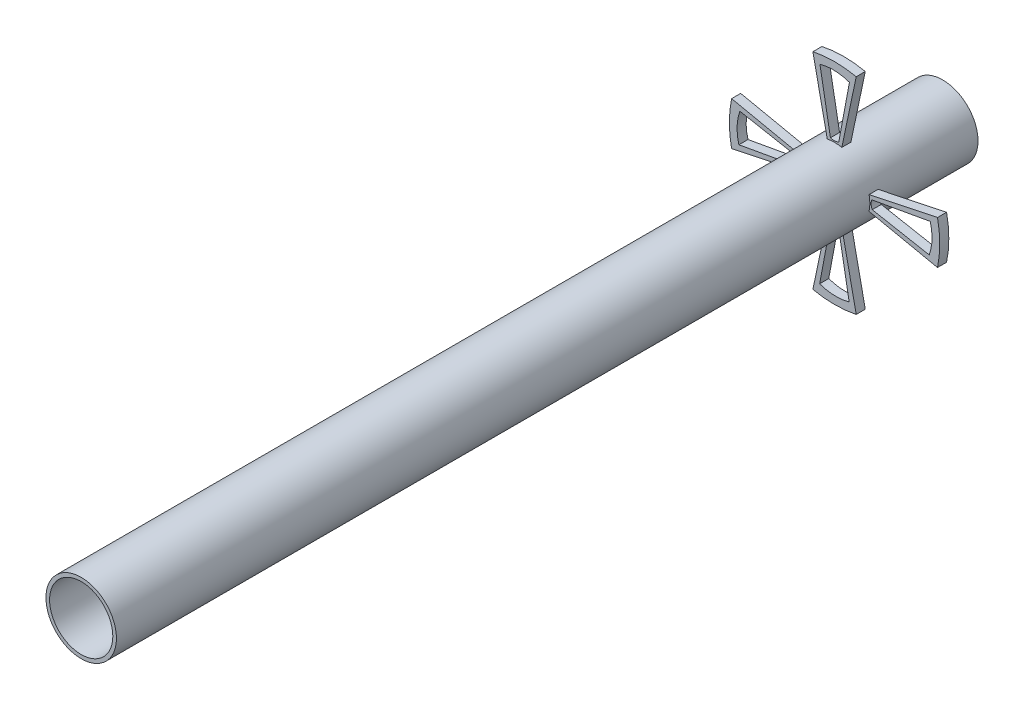
SolidWorks part; units mm, degrees
ref_plane "Front Plane" through (0, 0, 0) normal (0, 0, 1) x (1, 0, 0)
ref_plane "Top Plane" through (0, 0, 0) normal (0, 1, 0) x (1, 0, 0)
ref_plane "Right Plane" through (0, 0, 0) normal (1, 0, 0) x (0, 0, -1)
sketch "Sketch4" plane through (0, 0, 0) normal (0, 0, 1) x (1, 0, 0)
  line L0 (-95.0204, -20) -> (-283.5289, -59.6775)
  line L1 (-95.0204, 20) -> (-283.5289, 59.6775)
  line L2 (20, 95.0204) -> (59.6775, 283.5289)
  line L3 (-20, 95.0204) -> (-59.6775, 283.5289)
  line L4 (95.0204, -20) -> (283.5289, -59.6775)
  line L5 (95.0204, 20) -> (283.5289, 59.6775)
  line L6 (-20, -95.0204) -> (-59.6775, -283.5289)
  line L7 (20, -95.0204) -> (59.6775, -283.5289)
  line L8 (-102.4488, -11.3444) -> (-263.4403, -40.3434)
  line L9 (-103.7499, 11.6183) -> (-260.7282, 40.9886)
  line L10 (11.6183, 103.7499) -> (40.9886, 260.7282)
  line L11 (-11.3444, 102.4488) -> (-40.3434, 263.4403)
  line L12 (103.7499, -11.6183) -> (260.7282, -40.9886)
  line L13 (102.4488, 11.3444) -> (263.4403, 40.3434)
  line L14 (-11.6183, -103.7499) -> (-40.9886, -260.7282)
  line L15 (11.3444, -102.4488) -> (40.3434, -263.4403)
  arc A0 (-59.6775, -283.5289) -> (59.6775, -283.5289) centre (0, 0) ccw
  circle A1 centre (0, 0) radius 97.1024
  circle A2 centre (0, 0) radius 97.1024
  arc A3 (-59.6775, -283.5289) -> (59.6775, -283.5289) centre (0, 0) ccw
  circle A4 centre (0, 0) radius 97.1024
  arc A5 (-59.6775, -283.5289) -> (59.6775, -283.5289) centre (0, 0) ccw
  circle A6 centre (0, 0) radius 97.1024
  arc A7 (-59.6775, -283.5289) -> (59.6775, -283.5289) centre (0, 0) ccw
  arc A8 (-283.5289, 59.6775) -> (-283.5289, -59.6775) centre (0, 0) ccw
  arc A9 (-283.5289, 59.6775) -> (-283.5289, -59.6775) centre (0, 0) ccw
  arc A10 (-283.5289, 59.6775) -> (-283.5289, -59.6775) centre (0, 0) ccw
  arc A11 (-283.5289, 59.6775) -> (-283.5289, -59.6775) centre (0, 0) ccw
  arc A12 (59.6775, 283.5289) -> (-59.6775, 283.5289) centre (0, 0) ccw
  arc A13 (59.6775, 283.5289) -> (-59.6775, 283.5289) centre (0, 0) ccw
  arc A14 (59.6775, 283.5289) -> (-59.6775, 283.5289) centre (0, 0) ccw
  arc A15 (59.6775, 283.5289) -> (-59.6775, 283.5289) centre (0, 0) ccw
  arc A16 (283.5289, -59.6775) -> (283.5289, 59.6775) centre (0, 0) ccw
  arc A17 (283.5289, -59.6775) -> (283.5289, 59.6775) centre (0, 0) ccw
  arc A18 (283.5289, -59.6775) -> (283.5289, 59.6775) centre (0, 0) ccw
  arc A19 (283.5289, -59.6775) -> (283.5289, 59.6775) centre (0, 0) ccw
  arc A20 (-103.7499, 11.6183) -> (-102.4488, -11.3444) centre (-130.7634, -1.4306) cw
  arc A21 (-263.4403, -40.3434) -> (-260.7282, 40.9886) centre (-134.5091, -3.9314) cw
  arc A22 (-40.3434, 263.4403) -> (40.9886, 260.7282) centre (-3.9314, 134.5091) cw
  arc A23 (11.6183, 103.7499) -> (-11.3444, 102.4488) centre (-1.4306, 130.7634) cw
  arc A24 (263.4403, 40.3434) -> (260.7282, -40.9886) centre (134.5091, 3.9314) cw
  arc A25 (103.7499, -11.6183) -> (102.4488, 11.3444) centre (130.7634, 1.4306) cw
  arc A26 (40.3434, -263.4403) -> (-40.9886, -260.7282) centre (3.9314, -134.5091) cw
  arc A27 (-11.6183, -103.7499) -> (11.3444, -102.4488) centre (1.4306, -130.7634) cw
  circle A28 centre (0, 0) radius 290
  point P6 (-97.1024, 0)
  point P7 (-289.7414, 0)
  dimension "D1" = 20
  dimension "D8" = 4
  dimension "D9" = 192.639
  dimension "D2" = 20
  dimension "D3" = 60
  dimension "D4" = 60
  dimension "D5" = 4
  dimension "D6" = 10
  dimension "D7" = 10
extrude "Boss-Extrude5" add sketch "Sketch4" along normal blind 25 contours L1 A8 L0 A1 L8 A21 L9 A20 | L2 A12 L3 A1 L10 A23 L11 A22 | L4 A16 L5 A1 L12 A25 L13 A24 | A1 L6 A0 L7 L14 A27 L15 A26
sketch "Sketch5" plane through (0, 0, 0) normal (0, 0, 1) x (1, 0, 0)
  circle A0 centre (0, 0) radius 97.1024
  circle A1 centre (0, 0) radius 87.1024
  dimension "D1" = 10
  dimension "D2" = 194.2047
extrude "Boss-Extrude6" add sketch "Sketch5" along normal blind 2100 and the other way blind 273
